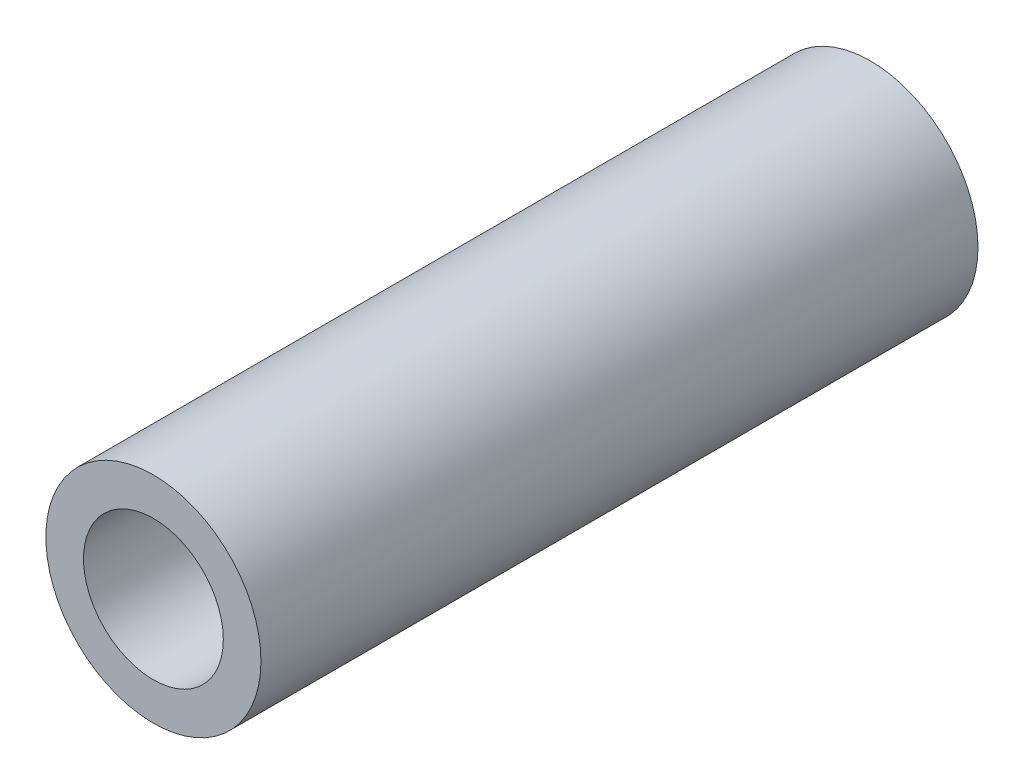
SolidWorks part; units mm, degrees
ref_plane "Płaszczyzna przednia" through (0, 0, 0) normal (0, 0, 1) x (1, 0, 0)
ref_plane "Płaszczyzna górna" through (0, 0, 0) normal (0, 1, 0) x (1, 0, 0)
ref_plane "Płaszczyzna prawa" through (0, 0, 0) normal (1, 0, 0) x (0, 0, -1)
sketch "Szkic1" plane through (0, 0, 0) normal (0, 0, 1) x (1, 0, 0)
  circle A0 centre (0, 0) radius 3
  circle A1 centre (0, 0) radius 1.95
  dimension "D1" = 6
  dimension "D2" = 3.9
extrude "Dodanie-wyciągnięcie1" add sketch "Szkic1" along normal blind 20
